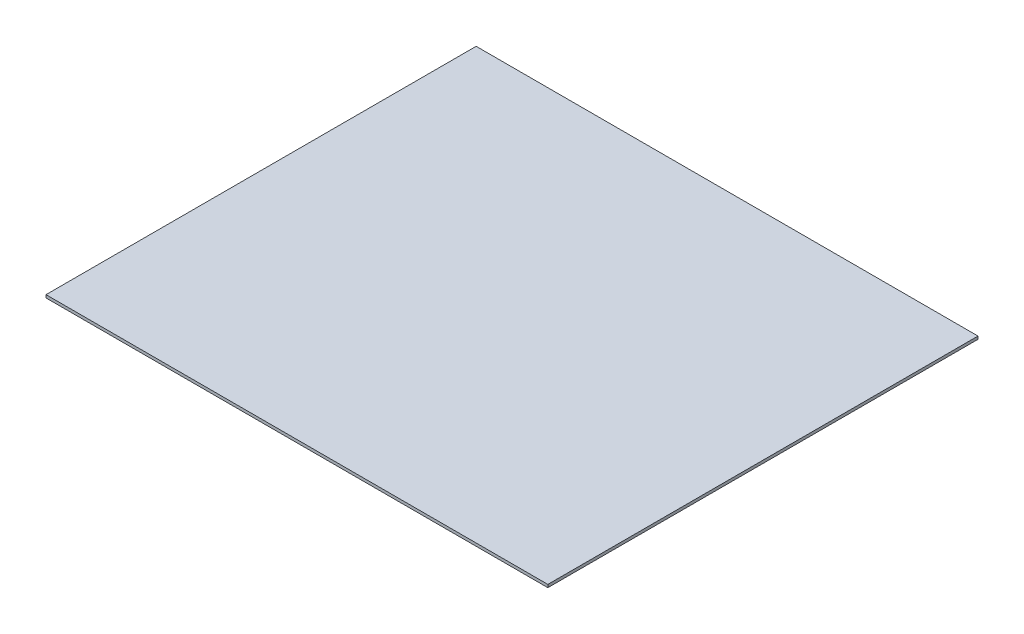
SolidWorks part; units mm, degrees
ref_plane "Front Plane" through (0, 0, 0) normal (0, 0, 1) x (1, 0, 0)
ref_plane "Top Plane" through (0, 0, 0) normal (0, 1, 0) x (1, 0, 0)
ref_plane "Right Plane" through (0, 0, 0) normal (1, 0, 0) x (0, 0, -1)
sketch "Sketch1" plane through (0, 0, 0) normal (0, 1, 0) x (1, 0, 0)
  line L1 (0, 0) -> (700, 0)
  line L2 (0, 0) -> (0, 600)
  line L3 (0, 600) -> (700, 600)
  line L4 (700, 0) -> (700, 600)
  dimension "D1" = 700
  dimension "D2" = 600
extrude "Boss-Extrude1" add sketch "Sketch1" along normal blind 4
